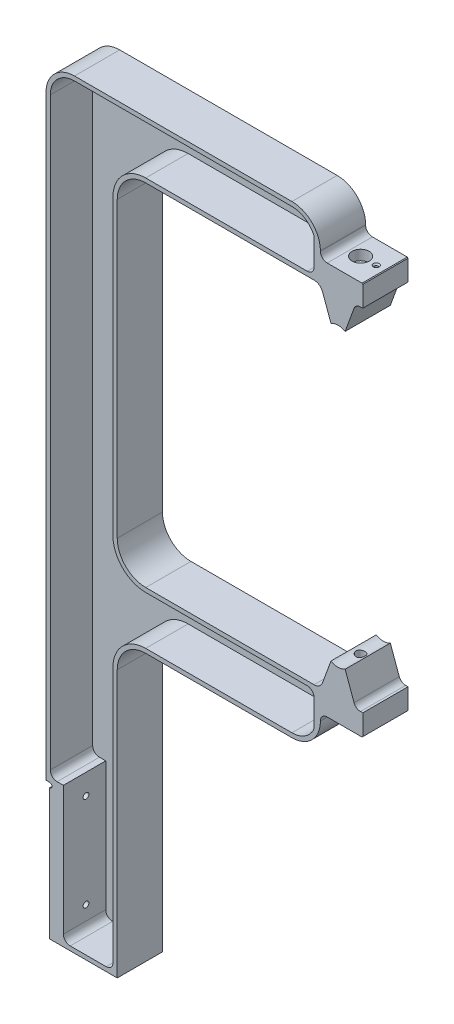
SolidWorks part; units mm, degrees
material "6061-T6 (SS)"
ref_plane "Front Plane" through (0, 0, 0) normal (0, 0, 1) x (1, 0, 0)
ref_plane "Top Plane" through (0, 0, 0) normal (0, 1, 0) x (1, 0, 0)
ref_plane "Right Plane" through (0, 0, 0) normal (1, 0, 0) x (0, 0, -1)
sketch "Sketch1" plane through (0, 0, 0) normal (0, 0, 1) x (1, 0, 0)
  line L0 (-158, 0) -> (-73.1133, 0) construction
  line L1 (-158, 0) -> (-158, 41.5899) construction
  line L2 (-158, 94) -> (27.4245, 94) construction
  line L3 (-313, -123) -> (-176.365, -123)
  line L4 (-158, -94) -> (27.4245, -94) construction
  line L5 (-170.375, -163) -> (-313, -163)
  line L6 (-170.375, -138) -> (-170.375, -163)
  line L7 (-170.375, 138) -> (-170.375, 163)
  line L8 (-170.375, 163) -> (-363, 163)
  line L9 (-363, 163) -> (-363, -163)
  line L10 (-313, -123) -> (-313, 123)
  line L11 (-313, 123) -> (-176.365, 123)
  line L12 (-145.625, -138) -> (-170.375, -138)
  line L13 (-145.625, -123) -> (-145.625, -138) construction
  line L14 (-176.365, -123) -> (-170.375, -123)
  line L15 (-162.9768, -102.6736) -> (-170.375, -123)
  line L16 (-153.0232, -102.6736) -> (-145.625, -123)
  line L17 (-363, -163) -> (-363, -370.4)
  line L21 (-313, -370.4) -> (-313, -163)
  line L22 (0, 0) -> (0, 64.5627) construction
  line L23 (-158, 94) -> (-158, 122.2402) construction
  line L24 (-158, 94) -> (-148.0014, 121.4709) construction
  line L25 (-158, 94) -> (-169.4104, 125.3498) construction
  line L26 (-158, 94) -> (-158, 89) construction
  line L27 (-162.9768, 102.6736) -> (-170.375, 123)
  line L28 (-176.365, 123) -> (-170.375, 123)
  line L29 (-145.625, 123) -> (-145.625, 138) construction
  line L30 (-145.625, 138) -> (-170.375, 138)
  line L31 (-153.0232, 102.6736) -> (-145.625, 123)
  line L32 (-145.625, 138) -> (-140.625, 138)
  line L33 (-140.625, 138) -> (-140.625, 123)
  line L34 (-145.625, 123) -> (-140.625, 123)
  line L35 (-145.625, -123) -> (-140.625, -123)
  line L36 (-140.625, -138) -> (-140.625, -123)
  line L37 (-145.625, -138) -> (-140.625, -138)
  line L38 (-313, -370.4) -> (-363, -370.4)
  arc A0 (-162.9768, -102.6736) -> (-153.0232, -102.6736) centre (-158, -94) ccw
  circle A2 centre (0, 0) radius 215.02 construction
  arc A3 (-162.9768, 102.6736) -> (-153.0232, 102.6736) centre (-158, 94) cw
  point P6 (-363, 0)
  point P10 (-313, 0)
  dimension "D12" = 430.04
  dimension "D15" = 10
  dimension "D2" = 94
  dimension "D3" = 44
  dimension "D5" = 50
  dimension "D6" = 40
  dimension "D7" = 155
  dimension "D10" = 5
  dimension "D11" = 158
  dimension "D13" = 40
  dimension "D14" = 20
  dimension "D16" = 29
  dimension "D17" = 5
  dimension "D18" = 207.4
extrude "Boss-Extrude1" add sketch "Sketch1" along normal mid plane 31.75
sketch "Sketch13" plane through (0, 0, 15.875) normal (0, 0, 1) x (1, 0, 0)
  line L1 (-360.46, -275.15) -> (-363, -275.15)
  line L2 (-360.46, -275.15) -> (-360.46, -370.4)
  line L3 (-360.46, -370.4) -> (-363, -370.4)
  line L4 (-363, -275.15) -> (-363, -370.4)
  line L6 (-363, 163) -> (-363, -370.4) construction
  line L7 (-363, -370.4) -> (-313, -370.4) construction
  dimension "D1" = 95.25
  dimension "D3" = 2.54
extrude "Cut-Extrude2" cut sketch "Sketch13" against normal through all
sketch "Sketch14" plane through (0, 0, 15.875) normal (0, 0, 1) x (1, 0, 0)
  line L1 (-360.46, -275.15) -> (-358.8598, -275.15)
  line L2 (-360.46, -275.15) -> (-360.46, -278.452)
  line L3 (-360.46, -278.452) -> (-358.8598, -278.452)
  line L4 (-358.8598, -275.15) -> (-358.8598, -278.452)
  dimension "D1" = 1.6002
  dimension "D2" = 3.302
extrude "Cut-Extrude3" cut sketch "Sketch14" against normal through all
fillet "Fillet4" radius 1.5875 2 edges at (-358.8598, -275.15, 0) (-358.8598, -278.452, 0)
fillet "Fillet1" radius 6.35 2 edges at (-170.375, -123, 0) (-170.375, 123, 0)
fillet "Fillet2" radius 20 6 edges at (-313, 123, 0) (-170.375, 163, 0) (-313, -123, 0) (-170.375, -163, 0) (-313, -163, 0) (-363, 163, 0)
fillet "Fillet3" radius 4.7625 4 edges at (-170.375, -138, 0) (-170.375, 138, 0) (-145.625, -123, 0) (-145.625, 123, 0)
hole_wizard "M6 Clearance Hole1" positions "Sketch9" profile "Sketch8" hole size "M6" standard "Ansi Metric"
sketch "Sketch9" plane through (0, 138, 0) normal (0, 1, 0) x (-1, 0, 0)
  point P0 (158, 0)
sketch "Sketch8" plane through (-158, 138, 0) normal (1, 0, 0) x (0, 0, 1)
  line L0 (0, 0) -> (0, 51.9608)
  line L1 (0, 51.9608) -> (3.2, 50.038)
  line L2 (3.2, 50.038) -> (3.2, 0)
  line L5 (3.2, 0) -> (0, 0)
  line L10 (0, 51.9608) -> (-3.2, 50.038) construction
  line L11 (0, -6.35) -> (0, 107.95) construction
  dimension "Hole Dia." = 6.4
  dimension "Hole Depth" = 50.038
  dimension "Drill Angle" = 118
sketch "Sketch10" plane through (0, 138, 0) normal (0, 1, 0) x (1, 0, 0)
  line L0 (-140.625, 0) -> (-154.8, 0) construction
  line L1 (-140.625, -15.875) -> (-140.625, 15.875) construction
  line L2 (0, 0) -> (0, -39.1153) construction
  circle A0 centre (-158, 0) radius 3.2 construction
  circle A1 centre (-158, 0) radius 6
  point P8 (-147, 0)
  dimension "D2" = 12
  dimension "D1" = 147
extrude "Cut-Extrude1" cut sketch "Sketch10" against normal blind 7
hole_wizard "#4-40 Tapped Hole1" positions "Sketch12" profile "Sketch11" tap size "#4-40" standard "Ansi Inch"
sketch "Sketch12" plane through (0, 138, 0) normal (0, 1, 0) x (-1, 0, 0)
  point P0 (147, 0)
sketch "Sketch11" plane through (-147, 138, 0) normal (1, 0, 0) x (0, 0, 1)
  line L0 (0, 0) -> (0, 8.2792)
  line L1 (0, 8.2792) -> (1.1303, 7.6)
  line L2 (1.1303, 7.6) -> (1.1303, 0.9271)
  line L3 (1.1303, 0.9271) -> (2.0574, 0)
  line L5 (2.0574, 0) -> (0, 0)
  line L6 (-1.1303, 0.9271) -> (-2.0574, 0) construction
  line L10 (0, 8.2792) -> (-1.1303, 7.6) construction
  line L11 (0, -6.35) -> (0, 107.95) construction
  dimension "Tap Drill Dia." = 2.2606
  dimension "Tap Drill Depth" = 7.6
  dimension "Near C'Sink Dia." = 4.1148
  dimension "Near C'Sink Angle" = 90
  dimension "Drill Angle" = 118
cosmetic thread "Hole Thread1" parameters "D1"=5.69, "D2"=2.8448
mirror "Mirror1" about plane through (0, 0, 0) normal (0, 1, 0) of "M6 Clearance Hole1"
chamfer "Chamfer1" distance 0.5 angle 45 2 edges at (-140.625, 138, 0) (-140.625, -138, 0)
sketch "Sketch15" plane through (-360.46, 0, 0) normal (-1, 0, 0) x (0, 0, 1)
  line L0 (0, 0) -> (0, -286.58) construction
  line L1 (-15.875, -370.4) -> (15.875, -370.4) construction
  line L4 (0, -286.58) -> (0, -352.62) construction
  line L7 (-15.875, -319.6) -> (-8.3812, -319.6) construction
  point P7 (0, -319.6)
  dimension "D1" = 33.02
  dimension "D2" = 50.8
hole_wizard "#10-32 Tapped Hole1" positions "Sketch17" profile "Sketch16" tap size "#10-32" standard "Ansi Inch"
sketch "Sketch17" plane through (-360.46, 0, 0) normal (-1, 0, 0) x (0, 0, 1)
  point P0 (0, -286.58)
  point P3 (0, -352.62)
sketch "Sketch16" plane through (-360.46, -286.58, 0) normal (0, 1, 0) x (0, 0, 1)
  line L0 (0, 0) -> (0, 13.2433)
  line L1 (0, 13.2433) -> (2.0193, 12.03)
  line L2 (2.0193, 12.03) -> (2.0193, 1.0287)
  line L3 (2.0193, 1.0287) -> (3.048, 0)
  line L5 (3.048, 0) -> (0, 0)
  line L6 (-2.0193, 1.0287) -> (-3.048, 0) construction
  line L10 (0, 13.2433) -> (-2.0193, 12.03) construction
  line L11 (0, -6.35) -> (0, 107.95) construction
  dimension "Tap Drill Dia." = 4.0386
  dimension "Tap Drill Depth" = 12.03
  dimension "Near C'Sink Dia." = 6.096
  dimension "Near C'Sink Angle" = 90
  dimension "Drill Angle" = 118
cosmetic thread "Hole Thread2" parameters "D1"=9.65, "D2"=4.826
cosmetic thread "Hole Thread3" parameters "D1"=9.65, "D2"=4.826
sketch "Sketch25" plane through (0, 0, 15.875) normal (0, 0, 1) x (1, 0, 0)
  line L4 (-190.375, 160) -> (-343, 160)
  line L5 (-360, 143) -> (-360, -275.15)
  line L6 (-190.375, 160) -> (-343, 160)
  line L7 (-360, 143) -> (-360, -272.15)
  line L12 (-174.8213, -126) -> (-293, -126)
  line L13 (-316, -103) -> (-316, 103)
  line L14 (-293, 126) -> (-174.8213, 126)
  line L15 (-174.8213, -126) -> (-293, -126)
  line L16 (-316, -103) -> (-316, 103)
  line L17 (-293, 126) -> (-174.8213, 126)
  line L22 (-350.808, -367.4) -> (-316, -367.4)
  line L23 (-360.46, -370.4) -> (-313, -370.4) construction
  line L24 (-293, -160) -> (-190.375, -160)
  line L25 (-316, -370.4) -> (-316, -183)
  line L26 (-293, -160) -> (-190.375, -160)
  line L27 (-360, -272.15) -> (-350.808, -272.15)
  line L28 (-350.808, -272.15) -> (-350.808, -367.4)
  line L29 (-316, -367.4) -> (-316, -183)
  line L36 (-360.4473, -275.15) -> (-363, -275.15) construction
  line L37 (-360.46, -370.4) -> (-360.46, -278.452) construction
  line L49 (-174.8213, 126) -> (-174.8213, 149.8617)
  line L50 (-174.8213, -126) -> (-174.8213, -149.8617)
  arc A4 (-173.375, 143) -> (-190.375, 160) centre (-190.375, 143) ccw
  arc A5 (-343, 160) -> (-360, 143) centre (-343, 143) ccw
  arc A6 (-174.8213, 149.8617) -> (-190.375, 160) centre (-190.375, 143) ccw
  arc A7 (-343, 160) -> (-360, 143) centre (-343, 143) ccw
  arc A10 (-316, -103) -> (-293, -126) centre (-293, -103) ccw
  arc A11 (-293, 126) -> (-316, 103) centre (-293, 103) ccw
  arc A12 (-316, -103) -> (-293, -126) centre (-293, -103) ccw
  arc A13 (-293, 126) -> (-316, 103) centre (-293, 103) ccw
  arc A18 (-190.375, -160) -> (-173.375, -143) centre (-190.375, -143) ccw
  arc A19 (-293, -160) -> (-316, -183) centre (-293, -183) ccw
  arc A20 (-190.375, -160) -> (-174.8213, -149.8617) centre (-190.375, -143) ccw
  arc A21 (-293, -160) -> (-316, -183) centre (-293, -183) ccw
  dimension "D5" = 3
  dimension "D6" = 9.652
  dimension "D3" = 3
  dimension "D4" = 3
  dimension "D1" = 3
  dimension "D2" = 3
extrude "Cut-Extrude7" cut sketch "Sketch25" against normal offset from surface (29.75 mm away) 2 up to face at (-226.2974, -57.9362, -15.875)
fillet "Fillet5" radius 4.7625 7 edges at (-174.8213, 126, 1) (-174.8213, -126, 1) (-360, -272.15, 1) (-174.8213, 149.8617, 1) (-350.808, -367.4, 1) (-316, -367.4, 1) (-174.8213, -149.8617, 1)
